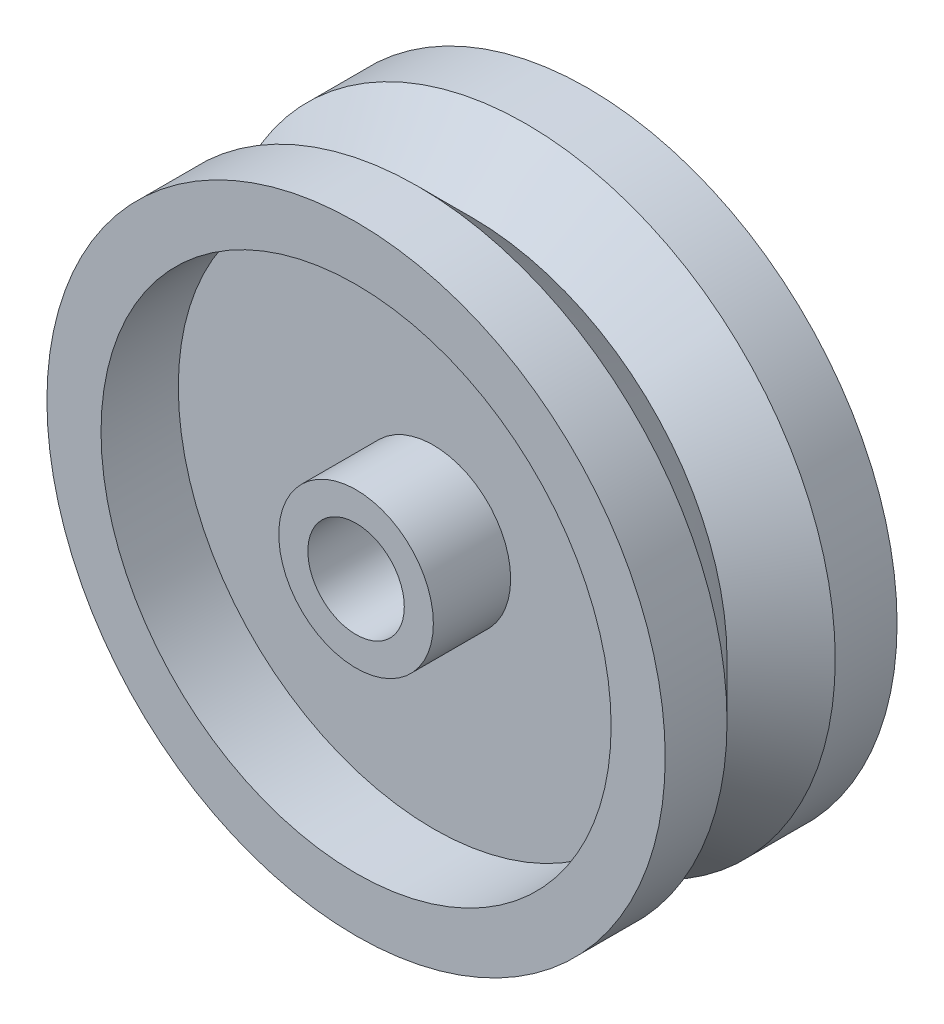
SolidWorks part; units mm, degrees
ref_plane "Front Plane" through (0, 0, 0) normal (0, 0, 1) x (1, 0, 0)
ref_plane "Top Plane" through (0, 0, 0) normal (0, 1, 0) x (1, 0, 0)
ref_plane "Right Plane" through (0, 0, 0) normal (1, 0, 0) x (0, 0, -1)
sketch "Sketch1" plane through (0, 0, 0) normal (1, 0, 0) x (0, 0, -1)
  line L0 (0, 0) -> (4, 0)
  line L1 (-8.7815, 20) -> (26.0354, 20) construction
  line L2 (0, 3.5) -> (5, 3.5)
  line L4 (0, 15) -> (5, 15)
  line L5 (5, 3.5) -> (5, 15)
  line L6 (0, 16.88) -> (0, 15)
  line L7 (0, 16.88) -> (15, 16.88)
  line L8 (7.5, -0.6682) -> (7.5, 18.9289) construction
  line L9 (15, 16.88) -> (15, 15)
  line L10 (15, 15) -> (10, 15)
  line L11 (15, 3.5) -> (10, 3.5)
  line L12 (10, 3.5) -> (10, 15)
  line L13 (15, 3.5) -> (15, 0)
  line L14 (0, 3.5) -> (0, 0)
  line L15 (7.5, 3.5) -> (4, 0)
  line L17 (11, 0) -> (7.5, 3.5)
  line L18 (11, 0) -> (15, 0)
  point P15 (-6.4916, 11.122)
  dimension "D1" = 15
  dimension "D2" = 20
  dimension "D3" = 16.5
  dimension "D4" = 5
  dimension "D5" = 3.12
  dimension "D6" = 5
  dimension "D7" = 90
  dimension "D9" = 4
revolve "Revolve1" add sketch "Sketch1" angle 360 about L1
